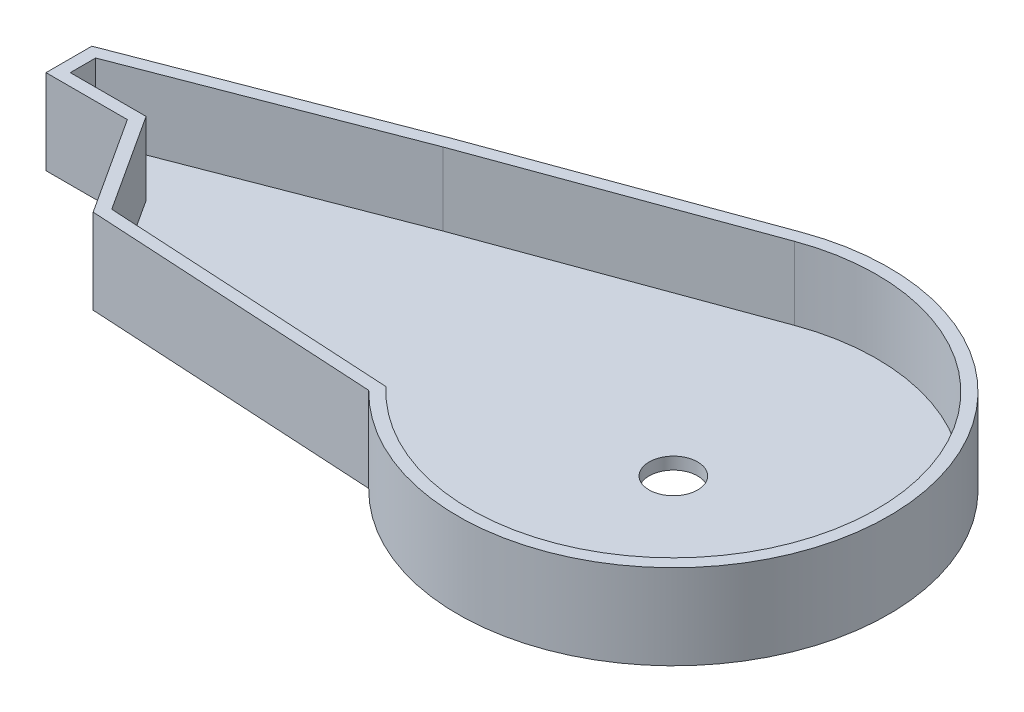
SolidWorks part; units mm, degrees
ref_plane "Front Plane" through (0, 0, 0) normal (0, 0, 1) x (1, 0, 0)
ref_plane "Top Plane" through (0, 0, 0) normal (0, 1, 0) x (1, 0, 0)
ref_plane "Right Plane" through (0, 0, 0) normal (1, 0, 0) x (0, 0, -1)
sketch "Sketch1" plane through (0, 0, 0) normal (0, 1, 0) x (1, 0, 0)
  line L0 (-32.154, -31.6034) -> (-93.2817, -28.139)
  line L1 (-15.4706, 42.3476) -> (-69.3585, 22.661)
  line L2 (-69.3585, 22.661) -> (-123.4963, 1.7985)
  line L3 (-123.4963, 1.7985) -> (-123.4963, -7.7935)
  line L4 (-123.4963, -7.7935) -> (-106.4706, -7.7935)
  line L5 (-106.4706, -7.7935) -> (-93.2817, -28.139)
  arc A0 (-32.154, -31.6034) -> (-15.4706, 42.3476) centre (0, 0) ccw
  circle A1 centre (0, 0) radius 5.08
  dimension "D1" = 90.17
  dimension "D2" = 10.16
  dimension "D3" = 50.8
extrude "Boss-Extrude1" add sketch "Sketch1" along normal blind 17.78
sketch "Sketch2" plane through (0, 17.78, 0) normal (0, 1, 0) x (1, 0, 0)
  line L12 (-14.599, 39.9618) -> (-68.466, 20.2828)
  line L13 (-68.466, 20.2828) -> (-120.9563, 0.0552)
  line L14 (-120.9563, 0.0552) -> (-120.9563, -5.2535)
  line L15 (-120.9563, -5.2535) -> (-105.0902, -5.2535)
  line L16 (-105.0902, -5.2535) -> (-91.8513, -25.676)
  line L17 (-91.8513, -25.676) -> (-31.0141, -29.124)
  line L18 (-14.599, 39.9618) -> (-68.466, 20.2828)
  line L19 (-68.466, 20.2828) -> (-120.9563, 0.0552)
  line L20 (-120.9563, 0.0552) -> (-120.9563, -5.2535)
  line L21 (-120.9563, -5.2535) -> (-105.0902, -5.2535)
  line L22 (-105.0902, -5.2535) -> (-91.8513, -25.676)
  line L23 (-91.8513, -25.676) -> (-31.0141, -29.124)
  arc A2 (-31.0141, -29.124) -> (-14.599, 39.9618) centre (0, 0) ccw
  arc A3 (-31.0141, -29.124) -> (-14.599, 39.9618) centre (0, 0) ccw
  dimension "D1" = 2.54
extrude "Cut-Extrude1" cut sketch "Sketch2" against normal blind 15.24
